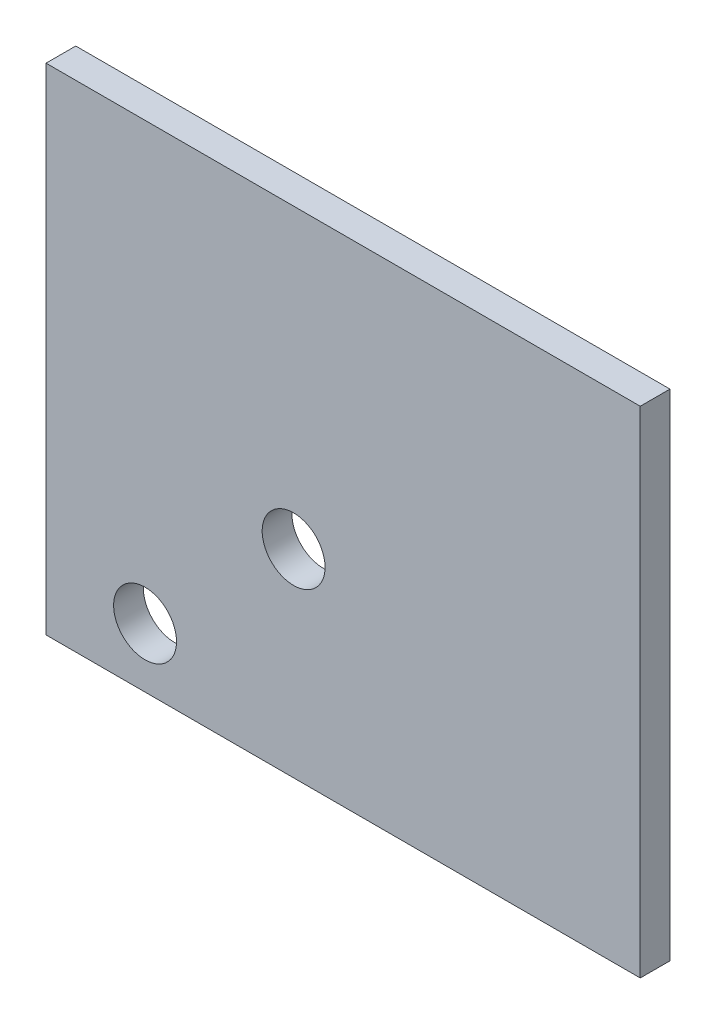
SolidWorks part; units mm, degrees
ref_plane "Front Plane" through (0, 0, 0) normal (0, 0, 1) x (1, 0, 0)
ref_plane "Top Plane" through (0, 0, 0) normal (0, 1, 0) x (1, 0, 0)
ref_plane "Right Plane" through (0, 0, 0) normal (1, 0, 0) x (0, 0, -1)
sketch "Sketch1" plane through (0, 0, 0) normal (0, 0, 1) x (1, 0, 0)
  line L1 (0, 0) -> (60, 0)
  line L2 (0, 0) -> (0, -50)
  line L3 (0, -50) -> (60, -50)
  line L4 (60, 0) -> (60, -50)
  dimension "D1" = 60
  dimension "D2" = 50
extrude "Boss-Extrude1" add sketch "Sketch1" along normal blind 3
sketch "Sketch2" plane through (0, 0, 3) normal (0, 0, 1) x (1, 0, 0)
  line L3 (0, -50) -> (60, -50) construction
  line L4 (0, 0) -> (0, -50) construction
  circle A0 centre (25, -30) radius 3.175
  circle A1 centre (10, -44) radius 3.175
  dimension "D4" = 6.35
  dimension "D3" = 25
  dimension "D5" = 6
  dimension "D6" = 10
extrude "Cut-Extrude1" cut sketch "Sketch2" against normal through all
